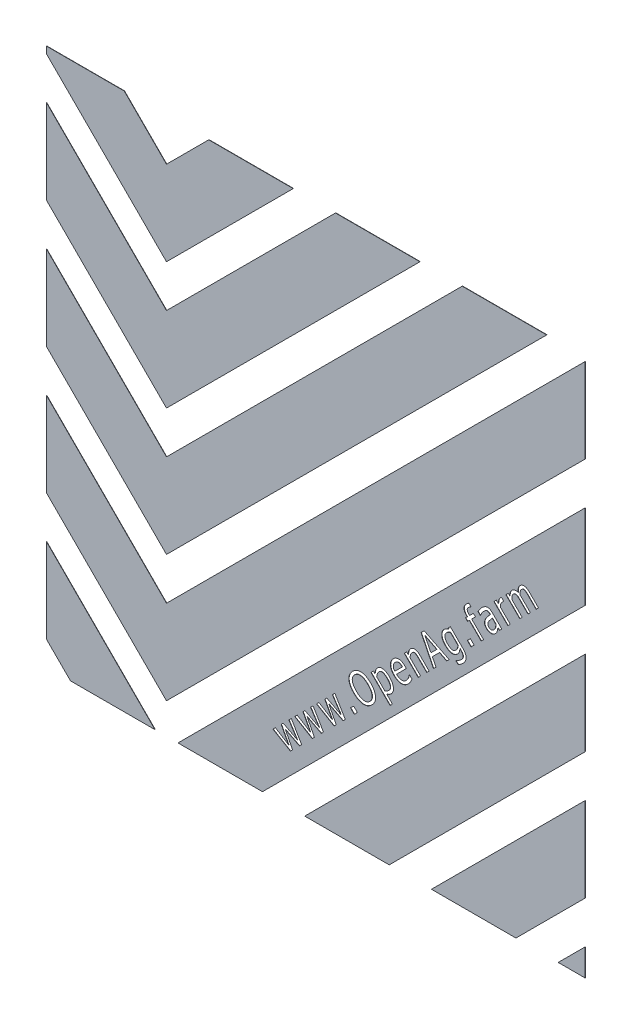
SolidWorks part; units mm, degrees
ref_plane "Front Plane" through (0, 0, 0) normal (0, 0, 1) x (1, 0, 0)
ref_plane "Top Plane" through (0, 0, 0) normal (0, 1, 0) x (1, 0, 0)
ref_plane "Right Plane" through (0, 0, 0) normal (1, 0, 0) x (0, 0, -1)
sketch "Sketch1" plane through (0, 0, 0) normal (0, 0, 1) x (1, 0, 0)
  line L1 (-114.4905, -114.3) -> (114.4905, -114.3)
  line L2 (-114.4905, -114.3) -> (-114.4905, 114.3)
  line L3 (-114.4905, 114.3) -> (114.4905, 114.3)
  line L4 (114.4905, -114.3) -> (114.4905, 114.3)
  line L5 (-114.4905, -114.3) -> (114.4905, 114.3) construction
  line L6 (-114.4905, 114.3) -> (114.4905, -114.3) construction
  point P0 (0, 0)
  dimension "D1" = 228.6
  dimension "D2" = 228.981
extrude "Boss-Extrude1" add sketch "Sketch1" along normal blind 0.127 contours L4 L3 L2 L1
sketch "Sketch2" plane through (0, 0, 0.127) normal (0, 0, 1) x (1, 0, 0)
  line L0 (-63.5, 130.5554) -> (-63.5, -134.9438) construction
  line L1 (-63.5, 114.3) -> (834.5256, 1012.3256)
  line L2 (-63.5, 96.3395) -> (834.5256, 994.3651)
  line L3 (186.1381, 243.1712) -> (298.7539, 130.5554) construction
  line L4 (298.7539, 130.5554) -> (204.8128, 130.5554) construction
  line L5 (-114.4905, 114.3) -> (114.4905, 114.3) construction
  line L6 (834.5256, 1012.3256) -> (834.5256, 994.3651)
  line L7 (834.5256, 958.4441) -> (834.5256, 940.4836)
  line L8 (-63.5, 42.458) -> (834.5256, 940.4836)
  line L9 (-63.5, 60.4185) -> (834.5256, 958.4441)
  line L10 (834.5256, 904.5625) -> (834.5256, 886.602)
  line L11 (-63.5, -11.4236) -> (834.5256, 886.602)
  line L12 (-63.5, 6.5369) -> (834.5256, 904.5625)
  line L13 (834.5256, 850.681) -> (834.5256, 832.7205)
  line L14 (-63.5, -65.3051) -> (834.5256, 832.7205)
  line L15 (-63.5, -47.3446) -> (834.5256, 850.681)
  line L16 (834.5256, 796.7995) -> (834.5256, 778.839)
  line L17 (-63.5, -119.1867) -> (834.5256, 778.839)
  line L18 (-63.5, -101.2261) -> (834.5256, 796.7995)
  line L19 (834.5256, 742.9179) -> (834.5256, 724.9574)
  line L20 (-63.5, -173.0682) -> (834.5256, 724.9574)
  line L21 (-63.5, -155.1077) -> (834.5256, 742.9179)
  line L22 (834.5256, 689.0364) -> (834.5256, 671.0759)
  line L23 (-63.5, -226.9497) -> (834.5256, 671.0759)
  line L24 (-63.5, -208.9892) -> (834.5256, 689.0364)
  line L25 (834.5256, 635.1549) -> (834.5256, 617.1943)
  line L26 (-63.5, -280.8313) -> (834.5256, 617.1943)
  line L27 (-63.5, -262.8708) -> (834.5256, 635.1549)
  line L28 (834.5256, 581.2733) -> (834.5256, 563.3128)
  line L29 (-63.5, -334.7128) -> (834.5256, 563.3128)
  line L30 (-63.5, -316.7523) -> (834.5256, 581.2733)
  line L31 (834.5256, 527.3918) -> (834.5256, 509.4313)
  line L32 (-63.5, -388.5943) -> (834.5256, 509.4313)
  line L33 (-63.5, -370.6338) -> (834.5256, 527.3918)
  line L34 (834.5256, 473.5102) -> (834.5256, 455.5497)
  line L35 (-63.5, -442.4759) -> (834.5256, 455.5497)
  line L36 (-63.5, -424.5154) -> (834.5256, 473.5102)
  line L37 (834.5256, 419.6287) -> (834.5256, 401.6682)
  line L38 (-63.5, -496.3574) -> (834.5256, 401.6682)
  line L39 (-63.5, -478.3969) -> (834.5256, 419.6287)
  line L40 (834.5256, 365.7472) -> (834.5256, 347.7867)
  line L41 (-63.5, -550.239) -> (834.5256, 347.7867)
  line L42 (-63.5, -532.2784) -> (834.5256, 365.7472)
  line L43 (834.5256, 311.8656) -> (834.5256, 293.9051)
  line L44 (-63.5, -604.1205) -> (834.5256, 293.9051)
  line L45 (-63.5, -586.16) -> (834.5256, 311.8656)
  line L46 (834.5256, 257.9841) -> (834.5256, 240.0236)
  line L47 (-63.5, -658.002) -> (834.5256, 240.0236)
  line L48 (-63.5, -640.0415) -> (834.5256, 257.9841)
  line L49 (834.5256, 204.1026) -> (834.5256, 186.142)
  line L50 (-63.5, -711.8836) -> (834.5256, 186.142)
  line L51 (-63.5, -693.9231) -> (834.5256, 204.1026)
  line L52 (834.5256, 150.221) -> (834.5256, 132.2605)
  line L53 (-63.5, -765.7651) -> (834.5256, 132.2605)
  line L54 (-63.5, -747.8046) -> (834.5256, 150.221)
  line L55 (834.5256, 96.3395) -> (834.5256, 78.379)
  line L56 (-63.5, -819.6466) -> (834.5256, 78.379)
  line L57 (-63.5, -801.6861) -> (834.5256, 96.3395)
  line L58 (-63.5, -801.6861) -> (-961.5256, 96.3395)
  line L59 (-63.5, -819.6466) -> (-961.5256, 78.379)
  line L60 (-961.5256, 96.3395) -> (-961.5256, 78.379)
  line L61 (-63.5, -747.8046) -> (-961.5256, 150.221)
  line L62 (-63.5, -765.7651) -> (-961.5256, 132.2605)
  line L63 (-961.5256, 150.221) -> (-961.5256, 132.2605)
  line L64 (-63.5, -693.9231) -> (-961.5256, 204.1026)
  line L65 (-63.5, -711.8836) -> (-961.5256, 186.142)
  line L66 (-961.5256, 204.1026) -> (-961.5256, 186.142)
  line L67 (-63.5, -640.0415) -> (-961.5256, 257.9841)
  line L68 (-63.5, -658.002) -> (-961.5256, 240.0236)
  line L69 (-961.5256, 257.9841) -> (-961.5256, 240.0236)
  line L70 (-63.5, -586.16) -> (-961.5256, 311.8656)
  line L71 (-63.5, -604.1205) -> (-961.5256, 293.9051)
  line L72 (-961.5256, 311.8656) -> (-961.5256, 293.9051)
  line L73 (-63.5, -532.2784) -> (-961.5256, 365.7472)
  line L74 (-63.5, -550.239) -> (-961.5256, 347.7867)
  line L75 (-961.5256, 365.7472) -> (-961.5256, 347.7867)
  line L76 (-63.5, -478.3969) -> (-961.5256, 419.6287)
  line L77 (-63.5, -496.3574) -> (-961.5256, 401.6682)
  line L78 (-961.5256, 419.6287) -> (-961.5256, 401.6682)
  line L79 (-63.5, -424.5154) -> (-961.5256, 473.5102)
  line L80 (-63.5, -442.4759) -> (-961.5256, 455.5497)
  line L81 (-961.5256, 473.5102) -> (-961.5256, 455.5497)
  line L82 (-63.5, -370.6338) -> (-961.5256, 527.3918)
  line L83 (-63.5, -388.5943) -> (-961.5256, 509.4313)
  line L84 (-961.5256, 527.3918) -> (-961.5256, 509.4313)
  line L85 (-63.5, -316.7523) -> (-961.5256, 581.2733)
  line L86 (-63.5, -334.7128) -> (-961.5256, 563.3128)
  line L87 (-961.5256, 581.2733) -> (-961.5256, 563.3128)
  line L88 (-63.5, -262.8708) -> (-961.5256, 635.1549)
  line L89 (-63.5, -280.8313) -> (-961.5256, 617.1943)
  line L90 (-961.5256, 635.1549) -> (-961.5256, 617.1943)
  line L91 (-63.5, -208.9892) -> (-961.5256, 689.0364)
  line L92 (-63.5, -226.9497) -> (-961.5256, 671.0759)
  line L93 (-961.5256, 689.0364) -> (-961.5256, 671.0759)
  line L94 (-63.5, -155.1077) -> (-961.5256, 742.9179)
  line L95 (-63.5, -173.0682) -> (-961.5256, 724.9574)
  line L96 (-961.5256, 742.9179) -> (-961.5256, 724.9574)
  line L97 (-63.5, -101.2261) -> (-961.5256, 796.7995)
  line L98 (-63.5, -119.1867) -> (-961.5256, 778.839)
  line L99 (-961.5256, 796.7995) -> (-961.5256, 778.839)
  line L100 (-63.5, -47.3446) -> (-961.5256, 850.681)
  line L101 (-63.5, -65.3051) -> (-961.5256, 832.7205)
  line L102 (-961.5256, 850.681) -> (-961.5256, 832.7205)
  line L103 (-63.5, 6.5369) -> (-961.5256, 904.5625)
  line L104 (-63.5, -11.4236) -> (-961.5256, 886.602)
  line L105 (-961.5256, 904.5625) -> (-961.5256, 886.602)
  line L106 (-63.5, 60.4185) -> (-961.5256, 958.4441)
  line L107 (-63.5, 42.458) -> (-961.5256, 940.4836)
  line L108 (-961.5256, 958.4441) -> (-961.5256, 940.4836)
  line L109 (-63.5, 96.3395) -> (-961.5256, 994.3651)
  line L110 (-63.5, 114.3) -> (-961.5256, 1012.3256)
  line L111 (-961.5256, 1012.3256) -> (-961.5256, 994.3651)
  line L112 (834.5256, 42.458) -> (834.5256, 24.4974)
  line L113 (-63.5, -873.5282) -> (834.5256, 24.4974)
  line L114 (-63.5, -855.5677) -> (834.5256, 42.458)
  line L115 (834.5256, -11.4236) -> (834.5256, -29.3841)
  line L116 (-63.5, -927.4097) -> (834.5256, -29.3841)
  line L117 (-63.5, -909.4492) -> (834.5256, -11.4236)
  line L118 (-63.5, -909.4492) -> (-961.5256, -11.4236)
  line L119 (-63.5, -927.4097) -> (-961.5256, -29.3841)
  line L120 (-961.5256, -11.4236) -> (-961.5256, -29.3841)
  line L121 (-63.5, -855.5677) -> (-961.5256, 42.458)
  line L122 (-63.5, -873.5282) -> (-961.5256, 24.4974)
  line L123 (-961.5256, 42.458) -> (-961.5256, 24.4974)
  dimension "D1" = 63.5
  dimension "D2" = 45
  dimension "D3" = 12.7
  dimension "D4" = 1270
  dimension "D6" = 25.4
  dimension "D5" = 20
extrude "Cut-Extrude1" cut sketch "Sketch2" against normal through all
sketch "Sketch3" plane through (0, 0, 0.127) normal (0, 0, 1) x (1, 0, 0)
  line L0 (45.8991, -45.7086) -> (26.5537, -26.3632) construction
  line L1 (-12.4726, -95.1) -> (95.2905, 12.6631) construction
  line L2 (114.4905, 22.8828) -> (-22.6923, -114.3) construction
  line L3 (114.4905, 22.8828) -> (-22.6923, -114.3) construction
  text T0 "www.OpenAg.farm" font "Tahoma" height 11.43
  point P1 (41.409, -41.2185)
  dimension "D1" = 152.4
  dimension "D2" = 6.35
extrude "Cut-Extrude2" cut sketch "Sketch3" against normal through all
equation "\"Height\"= 32in"
equation "\"Width\"= 23in"
equation "\"Depth\"= 20in"
equation "\"Plexi\"= .121in"
equation "\"EBWidth\" = 9in"
equation "\"ComponentMountDia\"=0.1770"
equation "\"MagnetThickness\"= 0.125in"
equation "\"MagnetDiameter\"= 12mm"
equation "\"DoorPlexi\" = \"Plexi\""
equation "\"ShelfThickness\" = .1250in"
equation "\"BasePlateThickness\" = 0.5in"
equation "\"BasePlateWidth\" = \"Width\"+\"EBWidth\"-2*\"Plexi\""
equation "\"Boxsize\" = .75in"
equation "\"BoxsizeHalf\" = \"Boxsize\"/2"
equation "\"Boxinner\" = .625in"
equation "\"CornerCube\" = 0.75in"
equation "\"FingerLength\" = 1.125in"
equation "\"FingerWidth\" = .625in"
equation "\"Cutwidth\"= .016in"
equation "\"Earsize\"= 1in + \"Cutwidth\" /2"
equation "\"Slotsize\" = 1in - \"CutWidth\" / 2"
equation "\"InnerWidth\" = \"Width\" - 2* \"Plexi\""
equation "\"InnerHeight\" = \"Height\" -2 * \"Plexi\""
equation "\"InnerDepth\" = \"Depth\" - 2*\"Plexi\""
equation "\"FrontDoorGap\" = .1in"
equation "\"TopDepth\" = \"Depth\"-\"DoorPlexi\"-\"FrontDoorGap\""
equation "\"TopBarDepth\" = \"Depth\"-\"DoorPlexi\"-\"Plexi\"-2*\"MagnetThickness\"-2*\"CornerCube\""
equation "\"RearNumHoles\" = 4"
equation "\"RearHolesBorder\" = 2.25"
equation "\"RearHoleSpacing\" = (\"Width\" - 2*\"RearHolesBorder\") / (\"RearNumHoles\"-1)"
equation "\"RearBarLength\" = (\"InnerWidth\"-2*\"CornerCube\")"
equation "\"RearTopNumHoles\" = 4"
equation "\"RearTopHolesBorder\" = 3.1"
equation "\"RearTopHolesSpacing\" = (\"Width\" - 2*\"RearTopHolesBorder\") / (\"RearTopNumHoles\"-1)"
equation "\"SideTopNumHoles\" = 4"
equation "\"SideTopHoleOffset\"=\"CornerCube\"+\"FingerLength\"+\"Plexi\"+.5"
equation "\"SideTopHoleSpacing\" = (\"TopBarDepth\"-2*\"SideTopHoleOffset\") / (\"SideTopNumHoles\"-1)"
equation "\"SideHorizNumHoles\" = 4"
equation "\"SideHorizHoleBorder\" = 1.50"
equation "\"SideHorizHoleSpacing\" = (\"TopBarDepth\"-2*\"SideHorizHoleBorder\") / (\"SideHorizNumHoles\"-1)"
equation "\"SideVertBarLength\"=\"Height\"-\"BasePlateThickness\"-2*\"CornerCube\"-\"Plexi\""
equation "\"SideVertNumHoles\" = 4"
equation "\"SideVertHolesBorder\" = \"CornerCube\"+\"FingerLength\"+1.50"
equation "\"SideVertHoleSpacing\" = (\"InnerHeight\" - 2*\"SideVertHolesBorder\") / (\"SideVertNumHoles\"-1)"
equation "\"RearSideVertNumHoles\" = 4"
equation "\"RearSideVertHolesBorder\" = 2.4"
equation "\"RearSideVertHoleSpacing\" = (\"InnerHeight\" - 2*\"RearSideVertHolesBorder\") / (\"RearSideVertNumHoles\"-1)"
equation "\"Rivet3_16Dia\" = .191in"
equation "\"RivetDia\" = .228in"
equation "\"BinderPostDia\" = .228in"
equation "\"SlotDepth\" = \"Plexi\" + 0.75in + .005in"
equation "\"SideSlotWidth\"   = \"Plexi\"+.005in"
equation "\"SidePanelVertSpacing\" = (\"Height\"-2*(1.75-\"Plexi\")) / 5"
equation "\"BottomPanelSideHoleSpacing\" = (\"InnerDepth\"-2*(1.75-\"Plexi\")) / 4"
equation "\"CoolerDepth\" = 12in"
equation "\"ShelfGap\" = 0.5in"
equation "\"ShelfDepth\" = \"TopBarDepth\"+\"CornerCube\"-\"CoolerDepth\""
equation "\"ShelfBarDepth\"=\"ShelfDepth\"-2*\"CornerCube\""
equation "\"ShelfWidth\" = \"EBWidth\"-\"ShelfGap\""
equation "\"ShelfBarWidth\" = \"EBWidth\"-\"Boxsize\""
equation "\"ShelfBarWidthShort\" = \"ShelfBarWidth\"-\"Boxsize\"-\"ShelfGap\""
equation "\"ShelfHeight1\" = 13in"
equation "\"ShelfHeight2\" = 24in"
equation "\"IntakeWidth\"=4in"
equation "\"IntakeHeight\"=2in"
equation "\"ExhaustWidth\"=4in"
equation "\"ExhaustHeight\"=2in"
equation "\"VentSpacing\"=7in"
equation "\"VentVertLocation\"=12.75in"
equation "\"AngleBracketLengthShort\"=.625in"
equation "\"AngleBracketLengthLong\"=1in"
equation "\"AngleBracketWidth\"=.5in"
equation "\"AngleBracketThickness\"=.125in"
equation "\"AngleBracketHolePosShort\"=.358in"
equation "\"AngleBracketHolePosLong\"=.7in"
equation "\"AngleBracketHoleDia\"=\"Rivet3_16Dia\""
equation "\"ShelfBarAngleHole\"=\"ShelfGap\"+\"Boxsize\"+\"AngleBracketHolePosShort\""
equation "\"PSBracketThickness\" = .0641in"
equation "\"EBForwardMountOffset\" = 4.0in"
equation "\"EBForwardMount\" = 2*\"Boxsize\"+\"CoolerDepth\"+\"EBForwardMountOffset\""
equation "\"EBRearwardMountOffset\" = 1.5in"
equation "\"EBRearwardMount\"= \"Boxsize\"+\"EBRearwardMountOffset\""
equation "\"MagSealWidth\" = \"InnerWidth\""
equation "\"MagSealHeight\" = \"Height\"-\"BasePlateThickness\"-\"Plexi\""
equation "\"MagWidth\" = .500in"
equation "\"SiliconeSealOD\" = .3125in"
equation "\"SiliconeSealID\" = .1875in"
equation "\"SiliconeSealWidth\" = \"MagSealWidth\" - 2*\"MagWidth\"-\"SiliconeSealOD\""
equation "\"SiliconeSealHeigth\" = \"MagSealHeight\" - 2*\"MagWidth\"-\"SiliconeSealOD\""
equation "\"HooknLoopThick\" = .085in"
equation "\"HooknLoopWidth\" = 0.75in"
equation "\"HooknLoopHeigth\" = 0.75in"
equation "\"RivNutHeight\" = 0.015in"
equation "\"D2@Sketch1\"=\"EBWidth\"+\"RivNutHeight\""
